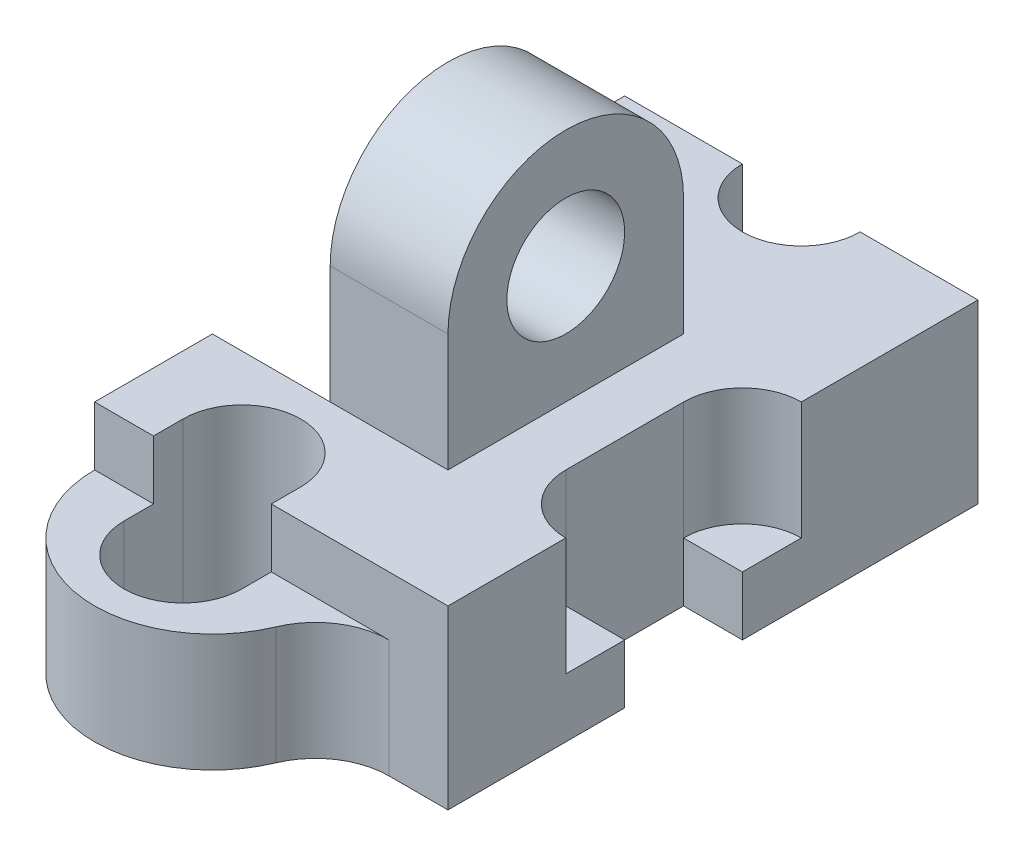
SolidWorks part; units mm, degrees
ref_plane "Front Plane" through (0, 0, 0) normal (0, 0, 1) x (1, 0, 0)
ref_plane "Top Plane" through (0, 0, 0) normal (0, 1, 0) x (1, 0, 0)
ref_plane "Right Plane" through (0, 0, 0) normal (1, 0, 0) x (0, 0, -1)
sketch "Sketch1" plane through (0, 0, 0) normal (0, 0, 1) x (1, 0, 0)
  line L1 (3, -1.5) -> (-3, -1.5)
  line L2 (3, -1.5) -> (3, 1.5)
  line L3 (3, 1.5) -> (-3, 1.5)
  line L4 (-3, -1.5) -> (-3, 1.5)
  line L5 (3, -1.5) -> (-3, 1.5) construction
  line L6 (3, 1.5) -> (-3, -1.5) construction
  point P0 (0, 0)
  dimension "D1" = 6
  dimension "D2" = 3
extrude "Boss-Extrude1" add sketch "Sketch1" along normal blind 9
sketch "Sketch2" plane through (0, -1.5, 0) normal (0, -1, 0) x (1, 0, 0)
  line L0 (-3, 9) -> (3, 9) construction
  line L1 (2, 9) -> (-3, 9)
  arc A0 (-3, 9) -> (0.8462, 9.7692) centre (-1, 9) cw
  arc A1 (0.8462, 9.7692) -> (2, 9) centre (2, 10.25) ccw
  point P0 (-1, 9)
  dimension "D1" = 2
  dimension "D2" = 1
extrude "Boss-Extrude2" add sketch "Sketch2" against normal blind 2
sketch "Sketch3" plane through (0, 0.5, 0) normal (0, 1, 0) x (1, 0, 0)
  line L0 (-1, -9.5) -> (-1, -8.5) construction
  line L1 (-2, -9.5) -> (-2, -8.5)
  line L2 (0, -9.5) -> (0, -8.5)
  arc A0 (-2, -9.5) -> (0, -9.5) centre (-1, -9.5) ccw
  arc A1 (0, -8.5) -> (-2, -8.5) centre (-1, -8.5) ccw
  arc A2 (-3, -9) -> (0.8462, -9.7692) centre (-1, -9) ccw construction
  point P2 (-1, -9)
  dimension "D4" = 0.5
  dimension "D1" = 1
  dimension "D2" = 1
  dimension "D3" = 0.5
extrude "Cut-Extrude1" cut sketch "Sketch3" against normal mid plane 5
sketch "Sketch4" plane through (0, -1.5, 0) normal (0, -1, 0) x (1, 0, 0)
  line L0 (3, 4) -> (2, 4)
  line L1 (3, 9) -> (3, 0) construction
  line L2 (2, 4) -> (2, 6)
  line L3 (2, 6) -> (3, 6)
  line L4 (3, 6) -> (3, 4)
  line L5 (2, 9) -> (3, 9) construction
  dimension "D1" = 3
  dimension "D2" = 2
  dimension "D3" = 1
extrude "Cut-Extrude2" cut sketch "Sketch4" against normal blind 1
sketch "Sketch5" plane through (0, 1.5, 0) normal (0, 1, 0) x (1, 0, 0)
  line L0 (3, -4) -> (3, -6) construction
  line L1 (3, -9) -> (3, 0) construction
  line L2 (4, -4) -> (4, -6)
  line L3 (2, -4) -> (2, -6)
  arc A0 (4, -4) -> (2, -4) centre (3, -4) ccw
  arc A1 (2, -6) -> (4, -6) centre (3, -6) ccw
  point P4 (3, -5)
  dimension "D1" = 2
  dimension "D2" = 3
  dimension "D3" = 1
extrude "Cut-Extrude3" cut sketch "Sketch5" against normal blind 2
sketch "Sketch6" plane through (0, -1.5, 0) normal (0, -1, 0) x (1, 0, 0)
  line L1 (-3, 0) -> (3, 0) construction
  line L2 (2, 0) -> (-2, 0)
  arc A0 (-2, 0) -> (2, 0) centre (0, 0) cw
  dimension "D1" = 1
extrude "Cut-Extrude4" cut sketch "Sketch6" against normal blind 1
sketch "Sketch7" plane through (0, 1.5, 0) normal (0, 1, 0) x (1, 0, 0)
  line L0 (3, 0) -> (-3, 0) construction
  line L1 (-1, 0) -> (1, 0)
  arc A0 (-1, 0) -> (1, 0) centre (0, 0) ccw
  dimension "D1" = 2
extrude "Cut-Extrude5" cut sketch "Sketch7" against normal through all
sketch "Sketch8" plane through (0, 1.5, 0) normal (0, 1, 0) x (1, 0, 0)
  line L0 (1, -3) -> (-1, -3)
  line L1 (-1, -3) -> (-1, -7)
  line L2 (-1, -7) -> (1, -7)
  line L3 (1, -7) -> (1, -3)
  line L4 (-3, -9) -> (-3, 0) construction
  line L5 (-2, -9) -> (-3, -9) construction
  point P6 (-2.5, -9)
  dimension "D1" = 2
  dimension "D2" = 2
  dimension "D3" = 4
  dimension "D4" = 2
extrude "Boss-Extrude3" add sketch "Sketch8" along normal blind 2
sketch "Sketch9" plane through (1, 0, 0) normal (1, 0, 0) x (0, 0, -1)
  line L0 (-7, 3.5) -> (-3, 3.5) construction
  line L1 (-3, 3.5) -> (-3, 1.5) construction
  line L2 (-3, 3.5) -> (-7, 3.5)
  arc A0 (-7, 3.5) -> (-3, 3.5) centre (-5, 3.5) cw
extrude "Boss-Extrude4" add sketch "Sketch9" against normal blind 2
sketch "Sketch10" plane through (1, 0, 0) normal (1, 0, 0) x (0, 0, -1)
  circle A0 centre (-5, 3.5) radius 1
  dimension "D1" = 2
extrude "Cut-Extrude6" cut sketch "Sketch10" against normal through all
sketch "Sketch11" plane through (0, 1.5, 0) normal (0, 1, 0) x (1, 0, 0)
  line L0 (-1, -3) -> (-3, -3)
  line L1 (-3, -9) -> (-3, 0) construction
  line L2 (-3, -3) -> (-3, -7)
  line L3 (-3, -7) -> (-1, -7)
  line L4 (-1, -7) -> (-1, -3)
extrude "Cut-Extrude7" cut sketch "Sketch11" against normal blind 2
sketch "Sketch12" plane through (0, 0, 3) normal (0, 0, 1) x (1, 0, 0)
  line L0 (-1, 1.5) -> (-1, -0.5)
  line L1 (-1, -0.5) -> (-3, -0.5)
  line L2 (-3, -0.5) -> (-1, -0.5)
  arc A0 (-1, 1.5) -> (-3, -0.5) centre (-3, 1.5) cw
  line M3 (-3, -0.5) -> (-1, -0.5)
  line M4 (-1, -0.5) -> (-1, 1.5)
  dimension "D1" = 2
  dimension "D2" = 2
  dimension "D3" = 2
extrude "Boss-Extrude5" add sketch "Sketch12" along normal blind 4 contours A0 M4 M3
